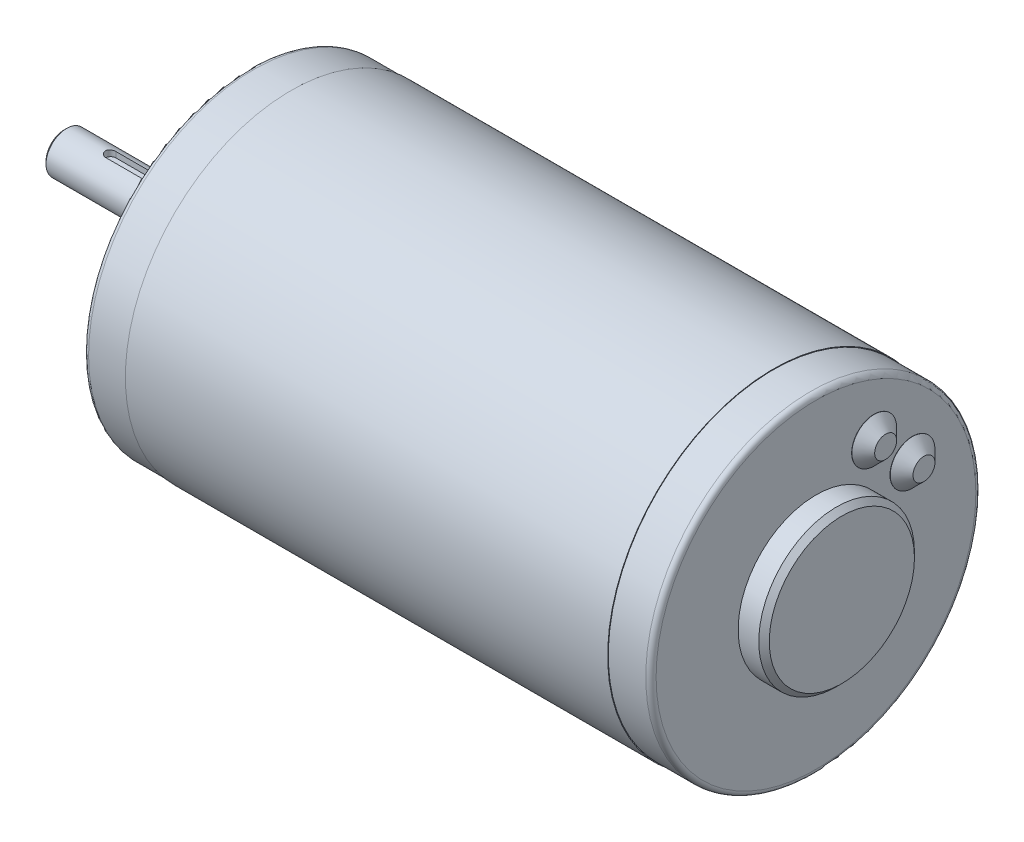
SolidWorks part; units mm, degrees
ref_plane "Front Plane" through (0, 0, 0) normal (0, 0, 1) x (1, 0, 0)
ref_plane "Top Plane" through (0, 0, 0) normal (0, 1, 0) x (1, 0, 0)
ref_plane "Right Plane" through (0, 0, 0) normal (1, 0, 0) x (0, 0, -1)
sketch "Sketch1" plane through (0, 0, 0) normal (0, 0, 1) x (1, 0, 0)
  line L0 (8.2296, 32.004) -> (8.2296, 0)
  line L1 (8.2296, 0) -> (101.3704, 0)
  line L2 (101.3704, 0) -> (101.3704, 32.004)
  line L3 (101.3704, 32.004) -> (8.2296, 32.004)
  line L4 (8.2296, 0) -> (101.3704, 0) construction
revolve "Revolve1" add sketch "Sketch1" angle 360 about L4
sketch "Sketch2" plane through (101.3704, 0, 0) normal (1, 0, 0) x (0, 0, -1)
  circle A0 centre (0, 0) radius 31.877
extrude "Boss-Extrude1" add sketch "Sketch2" along normal blind 8.2296
sketch "Sketch3" plane through (109.6, 0, 0) normal (1, 0, 0) x (0, 0, -1)
  circle A0 centre (0, 0) radius 15.0368
extrude "Boss-Extrude2" add sketch "Sketch3" along normal blind 3.984
sketch "Sketch4" plane through (113.584, 0, 0) normal (1, 0, 0) x (0, 0, -1)
  circle A0 centre (0, 0) radius 15.0368
extrude "Boss-Extrude3" add sketch "Sketch4" along normal blind 1.016 draft 45
sketch "Sketch5" plane through (8.2296, 0, 0) normal (-1, 0, 0) x (0, 0, 1)
  circle A0 centre (0, 0) radius 31.877
extrude "Boss-Extrude4" add sketch "Sketch5" along normal blind 8.2296
sketch "Sketch6" plane through (0, 0, 0) normal (-1, 0, 0) x (0, 0, 1)
  circle A0 centre (0, 0) radius 9.525
extrude "Boss-Extrude5" add sketch "Sketch6" along normal blind 4
sketch "Sketch7" plane through (-4, 0, 0) normal (-1, 0, 0) x (0, 0, 1)
  circle A0 centre (0, 0) radius 4
extrude "Boss-Extrude6" add sketch "Sketch7" along normal blind 31.6
imported_body "Surface-Imported1"
ref_plane "Plane1" through (0, 2.8, 0) normal (0, -1, 0) x (1, 0, 0)
sketch "Sketch8" plane through (0, 2.8, 0) normal (0, -1, 0) x (1, 0, 0)
  line L0 (-7.1, 1) -> (-26.6, 1)
  line L1 (-26.6, -1) -> (-7.1, -1)
  arc A0 (-7.1, -1) -> (-7.1, 1) centre (-7.1, 0) ccw
  arc A1 (-26.6, 1) -> (-26.6, -1) centre (-26.6, 0) ccw
extrude "Cut-Extrude1" cut sketch "Sketch8" against normal up to surface
ref_plane "Plane2" through (0, 0, -18.6071) normal (0, 0, 1) x (1, 0, 0)
sketch "Sketch9" plane through (0, 0, -18.6071) normal (0, 0, 1) x (1, 0, 0)
  line L0 (109.6, 15.5254) -> (109.6, 11.2074)
  line L1 (109.6, 11.2074) -> (111.8479, 11.2074)
  line L2 (111.8479, 11.2074) -> (111.8479, 13.3254)
  line L3 (111.8479, 13.3254) -> (109.6479, 15.5254)
  line L4 (109.6479, 15.5254) -> (109.6, 15.5254)
  line L5 (109.6, 11.2074) -> (111.8479, 11.2074) construction
revolve "Revolve2" add sketch "Sketch9" angle 360 about L5
ref_plane "Plane3" through (0, 0, -11.2074) normal (0, 0, 1) x (1, 0, 0)
sketch "Sketch10" plane through (0, 0, -11.2074) normal (0, 0, 1) x (1, 0, 0)
  line L0 (109.6, 22.9251) -> (109.6, 18.6071)
  line L1 (109.6, 18.6071) -> (111.8479, 18.6071)
  line L2 (111.8479, 18.6071) -> (111.8479, 20.7251)
  line L3 (111.8479, 20.7251) -> (109.6479, 22.9251)
  line L4 (109.6479, 22.9251) -> (109.6, 22.9251)
  line L5 (109.6, 18.6071) -> (111.8479, 18.6071) construction
revolve "Revolve3" add sketch "Sketch10" angle 360 about L5
hole_wizard "M3.5 Clearance Hole1" positions "Sketch12" profile "Sketch11" hole size "M3.5" standard "ANSI Metric"
sketch "Sketch12" plane through (0, 0, 0) normal (-1, 0, 0) x (0, 0, 1)
  point P0 (0, 25.4)
  point P1 (0, -25.4)
sketch "Sketch11" plane through (0, 25.4, 0) normal (0, 1, 0) x (0, 0, 1)
  line L0 (0, 0) -> (0, 14.8277)
  line L1 (0, 14.8277) -> (2.0193, 13.6144)
  line L2 (2.0193, 13.6144) -> (2.0193, 0)
  line L5 (2.0193, 0) -> (0, 0)
  line L10 (0, 14.8277) -> (-2.0193, 13.6144) construction
  line L11 (0, -6.35) -> (0, 107.95) construction
  dimension "Hole Dia." = 4.0386
  dimension "Hole Depth" = 13.6144
  dimension "Drill Angle" = 118
chamfer "Chamfer1" distance 1.016 angle 45 1 edges at (-4, 0, 9.525)
chamfer "Chamfer2" distance 0.5 angle 45 1 edges at (-35.6, 0, 4)
fillet "Fillet1" radius 1 2 edges at (109.6, 0, -31.877) (0, 0, 31.877)
